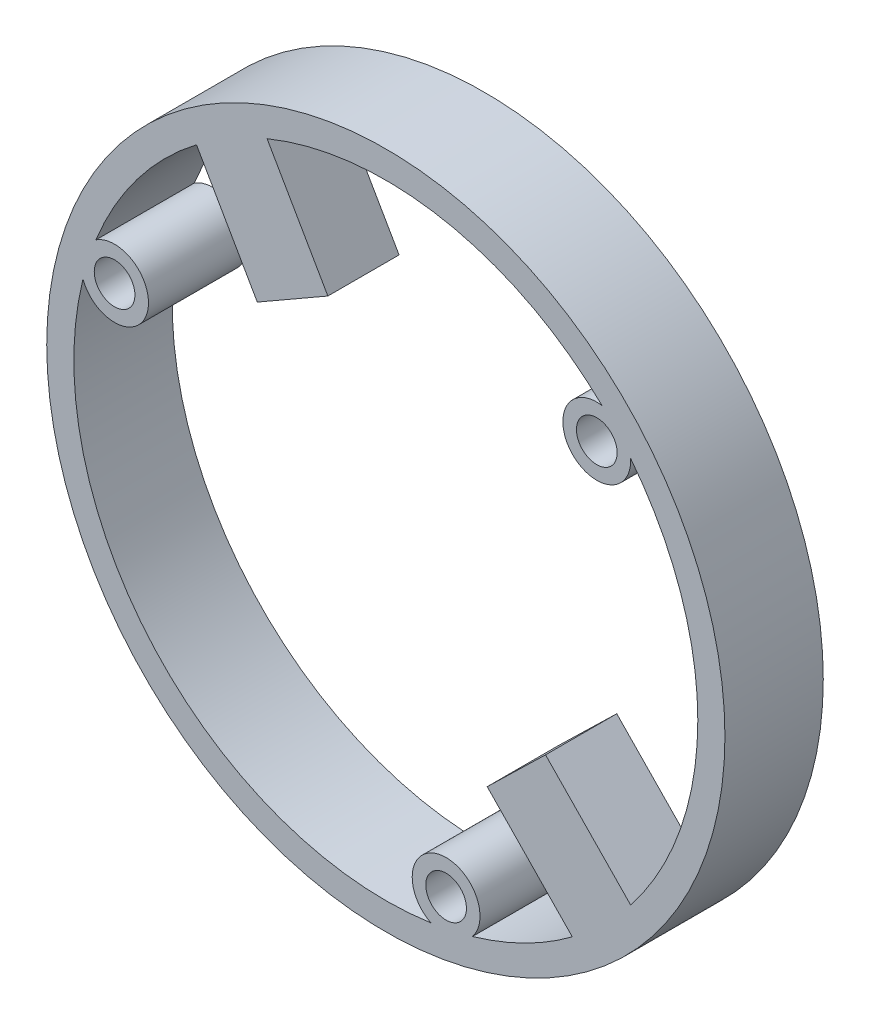
SolidWorks part; units mm, degrees
ref_plane "Front Plane" through (0, 0, 0) normal (0, 0, 1) x (1, 0, 0)
ref_plane "Top Plane" through (0, 0, 0) normal (0, 1, 0) x (1, 0, 0)
ref_plane "Right Plane" through (0, 0, 0) normal (1, 0, 0) x (0, 0, -1)
sketch "Sketch1" plane through (0, 0, 0) normal (0, 0, 1) x (1, 0, 0)
  circle A0 centre (0, 0) radius 25
  dimension "D1" = 50
extrude "Boss-Extrude1" add sketch "Sketch1" along normal blind 7.25
hole_wizard "Ø3.0mm Dowel Hole1" positions "Sketch2" profile "Sketch3" hole size "Ø3.0" standard "ANSI Metric" end condition through all
sketch "Sketch2" plane through (0, 0, 0) normal (0, 0, -1) x (-1, 0, 0)
  circle A0 centre (0, 0) radius 25 construction
  point P0 (-15.5528, 14.1106)
  dimension "D1" = 21
sketch "Sketch3" plane through (15.5528, 14.1106, 0) normal (1, 0, 0) x (0, 1, 0)
  line L0 (0, 0) -> (0, 7.25)
  line L1 (0, 7.25) -> (1.5, 7.25)
  line L2 (1.5, 7.25) -> (1.5, 0)
  line L5 (1.5, 0) -> (0, 0)
  line L11 (0, -6.35) -> (0, 107.95) construction
  dimension "Thru Hole Dia." = 3
  dimension "Thru Hole Depth" = 7.25
pattern_circular "CirPattern1" count 3 over 360 about axis through (0, 0, 0) along (0, 0, 1) of "Ø3.0mm Dowel Hole1"
sketch "Sketch4" plane through (0, 0, 0) normal (0, 0, -1) x (-1, 0, 0)
  line L6 (8.7551, 21.2685) -> (4.2729, 13.464)
  line L7 (13.9581, 18.2804) -> (9.4759, 10.4759)
  line L8 (4.2729, 13.464) -> (9.4759, 10.4759)
  line L9 (-18.0486, -14.2565) -> (-11.7741, -7.8044)
  line L10 (-13.7471, -18.4395) -> (-7.4726, -11.9874)
  line L11 (-11.7741, -7.8044) -> (-7.4726, -11.9874)
  arc A0 (-18.0486, 14.2565) -> (-18.0486, -14.2565) centre (0, 0) ccw
  arc A1 (-18.0486, 14.2565) -> (-15.9402, 16.5804) centre (-15.5528, 14.1106) ccw
  arc A2 (21.3708, 8.5023) -> (22.3292, 5.5144) centre (19.9966, 6.4139) ccw
  arc A3 (-3.3222, -22.7588) -> (-6.389, -22.0948) centre (-4.4437, -20.5245) ccw
  arc A4 (21.3708, 8.5023) -> (13.9581, 18.2804) centre (0, 0) ccw
  arc A5 (-3.3222, -22.7588) -> (22.3292, 5.5144) centre (0, 0) ccw
  arc A6 (-13.7471, -18.4395) -> (-6.389, -22.0948) centre (0, 0) ccw
  arc A7 (8.7551, 21.2685) -> (-15.9402, 16.5804) centre (0, 0) ccw
  point P11 (0, 0)
  point P12 (0, 0)
  point P19 (0, 0)
  point P22 (0, 0)
  dimension "D1" = 46
  dimension "D2" = 5
  dimension "D4" = 9
  dimension "D5" = 6
  dimension "D6" = 9
  dimension "D7" = 6
  dimension "D3" = 3
ref_plane "Plane1" through (0, 25, 0) normal (0, 1, 0) x (1, 0, 0)
ref_plane "Plane2" through (0, 23, 0) normal (0, 1, 0) x (1, 0, 0)
extrude "Cut-Extrude7" cut sketch "Sketch4" against normal through all
sketch "Sketch9" plane through (0, 0, 0) normal (0, 0, -1) x (-1, 0, 0)
  line L0 (-11.7741, -7.8044) -> (-18.0486, -14.2565)
  line L1 (-11.7741, -7.8044) -> (-7.4726, -11.9874)
  line L2 (-18.0486, -14.2565) -> (-13.7471, -18.4395)
  line L3 (-7.4726, -11.9874) -> (-13.7471, -18.4395)
  line L4 (4.2729, 13.464) -> (8.7551, 21.2685)
  line L5 (4.2729, 13.464) -> (9.4759, 10.4759)
  line L6 (8.7551, 21.2685) -> (13.9581, 18.2804)
  line L7 (9.4759, 10.4759) -> (13.9581, 18.2804)
  dimension "D1" = 6
  dimension "D2" = 6
extrude "Cut-Extrude9" cut sketch "Sketch9" against normal blind 2
